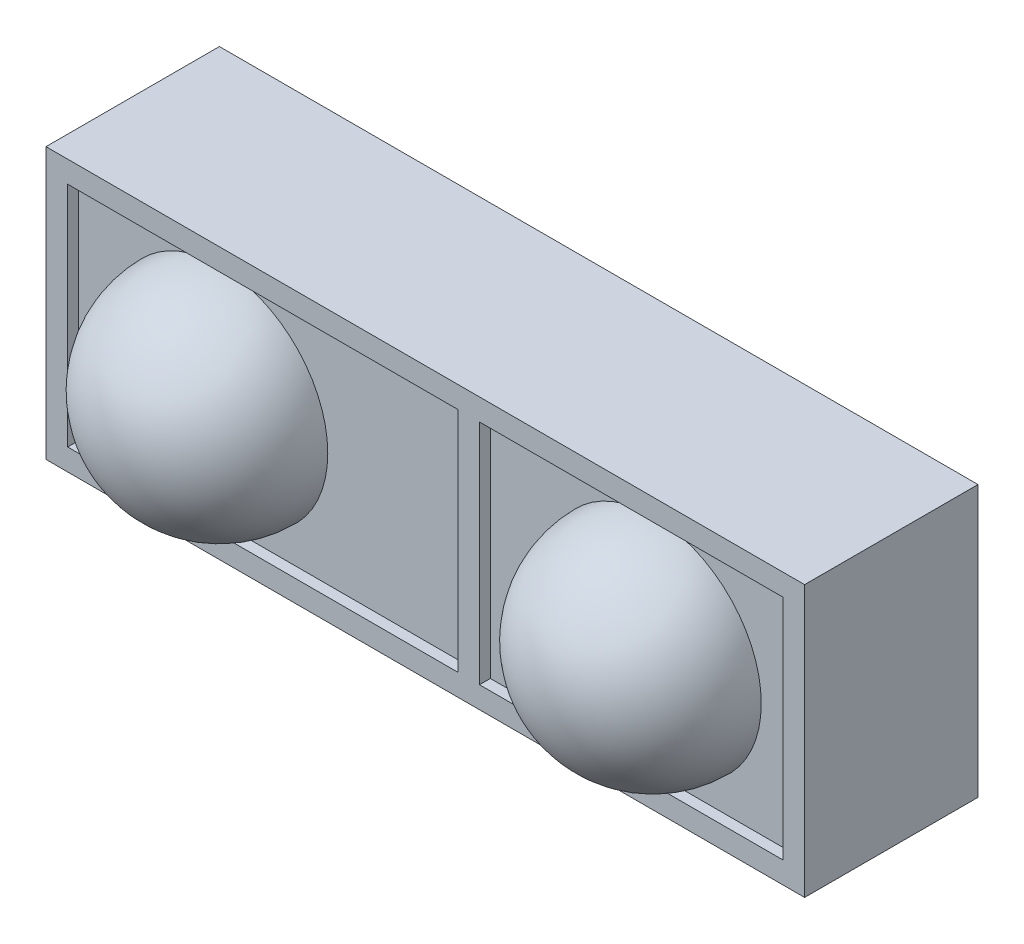
SolidWorks part; units mm, degrees
ref_plane "Front Plane" through (0, 0, 0) normal (0, 0, 1) x (1, 0, 0)
ref_plane "Top Plane" through (0, 0, 0) normal (0, 1, 0) x (1, 0, 0)
ref_plane "Right Plane" through (0, 0, 0) normal (1, 0, 0) x (0, 0, -1)
sketch "Sketch1" plane through (0, 0, 0) normal (0, 0, 1) x (1, 0, 0)
  line L0 (-3.5, 1.25) -> (3.5, -1.25) construction
  line L1 (-3.5, 1.25) -> (3.5, 1.25)
  line L2 (-3.5, 1.25) -> (-3.5, -1.25)
  line L3 (-3.5, -1.25) -> (3.5, -1.25)
  line L4 (3.5, 1.25) -> (3.5, -1.25)
  point P4 (0, 0)
  dimension "D1" = 7
  dimension "D2" = 2.5
extrude "Extrude1" add sketch "Sketch1" along normal blind 1.5
sketch "Sketch2" plane through (0, 0, 0) normal (0, 1, 0) x (1, 0, 0)
  line L0 (2, -3.0374) -> (2, 1.0492) construction
  line L1 (-3.5, -1.5) -> (3.5, -1.5) construction
  line L2 (2, -2.5) -> (2, -0.5)
  line L3 (2, -0.5) -> (2.0033, -0.4851)
  arc A0 (2, -2.5) -> (2, -0.5) centre (2, -1.5) ccw
  dimension "D2" = 1
  dimension "D1" = 2
revolve "Revolve1" add sketch "Sketch2" angle 360 about L0
pattern_linear "LPattern1" count 2 spacing 4 along (-1, 0, 0) of "Revolve1"
sketch "Sketch3" plane through (0, 0, 1.5) normal (0, 0, 1) x (1, 0, 0)
  line L4 (-3.5, 1.25) -> (-3.5, -1.25)
  line L5 (-3.5, -1.25) -> (3.5, -1.25)
  line L6 (3.5, -1.25) -> (3.5, 1.25)
  line L7 (3.5, 1.25) -> (-3.5, 1.25)
  line L8 (-3.5, 1.25) -> (-3.5, -1.25)
  line L9 (-3.5, -1.25) -> (3.5, -1.25)
  line L10 (3.5, -1.25) -> (3.5, 1.25)
  line L11 (3.5, 1.25) -> (-3.5, 1.25)
  line L12 (0.3, -1.05) -> (0.3, 1.05)
  line L13 (0.5, -1.05) -> (0.5, 1.05)
  line L14 (0.3, 1.05) -> (-3.3, 1.05)
  line L15 (0.5, -1.05) -> (3.3, -1.05)
  line L16 (-3.3, 1.05) -> (-3.3, -1.05)
  line L17 (-3.3, -1.05) -> (3.3, -1.05)
  line L18 (3.3, -1.05) -> (3.3, 1.05)
  line L19 (3.3, 1.05) -> (-3.3, 1.05)
  line L20 (-3.3, 1.05) -> (-3.3, -1.05)
  line L21 (-3.3, -1.05) -> (0.3, -1.05)
  line L22 (3.3, -1.05) -> (3.3, 1.05)
  line L23 (3.3, 1.05) -> (0.5, 1.05)
  dimension "D3" = 0.2
  dimension "D4" = 0.3
  dimension "D1" = 0
  dimension "D2" = 0.2
extrude "Extrude2" add sketch "Sketch3" along normal blind 0.1
